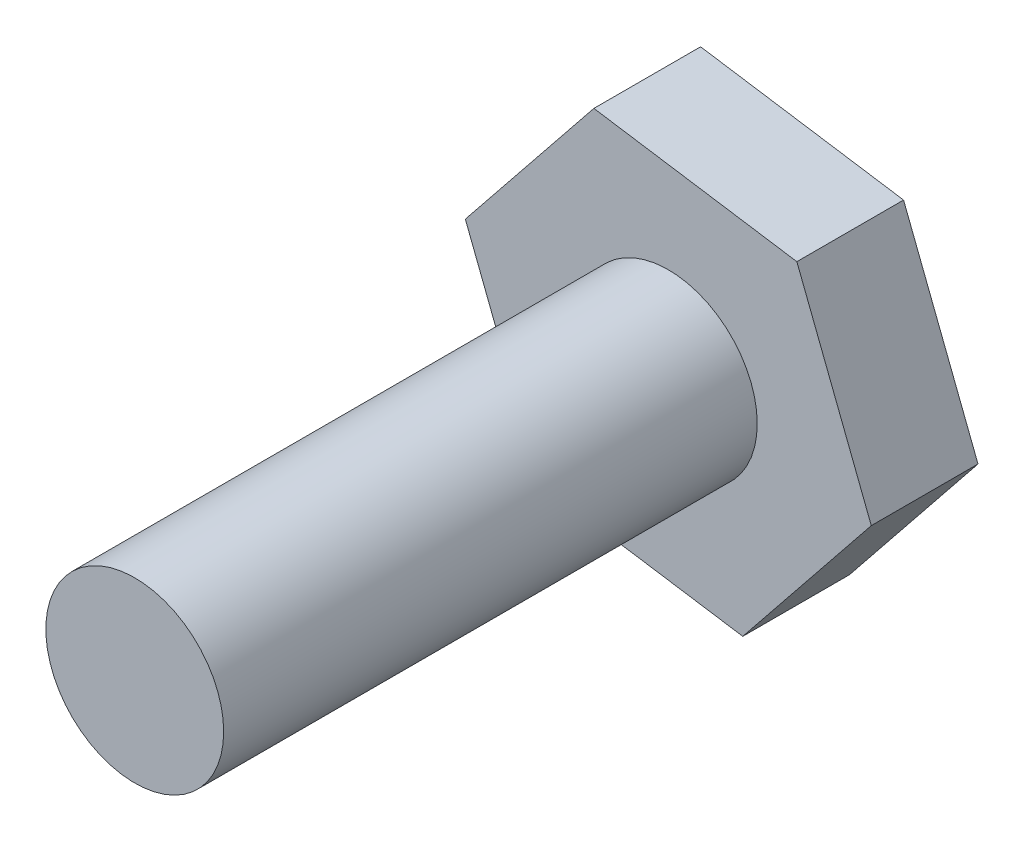
SolidWorks part; units mm, degrees
ref_plane "Alzado" through (0, 0, 0) normal (0, 0, 1) x (1, 0, 0)
ref_plane "Planta" through (0, 0, 0) normal (0, 1, 0) x (1, 0, 0)
ref_plane "Vista lateral" through (0, 0, 0) normal (1, 0, 0) x (0, 0, -1)
sketch "Croquis1" plane through (0, 0, 0) normal (0, 0, 1) x (1, 0, 0)
  line L1 (-54.3866, 4.2999) -> (-50.7729, 8.8026)
  line L2 (-50.7729, 8.8026) -> (-52.8655, 14.1835)
  line L3 (-52.8655, 14.1835) -> (-58.5718, 15.0617)
  line L4 (-58.5718, 15.0617) -> (-62.1855, 10.559)
  line L5 (-62.1855, 10.559) -> (-60.093, 5.1781)
  line L6 (-60.093, 5.1781) -> (-54.3866, 4.2999)
  circle A0 centre (-56.4792, 9.6808) radius 5 construction
  dimension "D1" = 5
extrude "Saliente-Extruir3" add sketch "Croquis1" along normal blind 3
sketch "Croquis3" plane through (0, 0, 0) normal (0, 0, 1) x (1, 0, 0)
  line L0 (-52.8655, 14.1835) -> (-58.5718, 15.0617) construction
  line L1 (-62.1855, 10.559) -> (-60.093, 5.1781) construction
  circle A0 centre (-56.4792, 9.6808) radius 2.5
  dimension "D1" = 5
  dimension "D2" = 5
extrude "Saliente-Extruir4" add sketch "Croquis3" along normal blind 18
